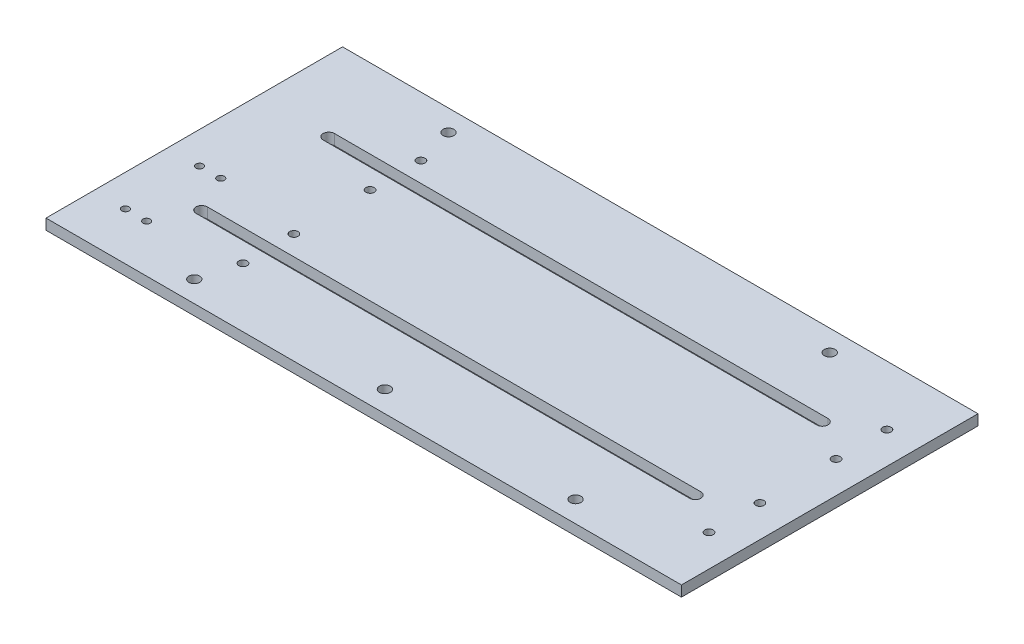
SolidWorks part; units mm, degrees
material "6061-T6 (SS)"
ref_plane "Front Plane" through (0, 0, 0) normal (0, 0, 1) x (1, 0, 0)
ref_plane "Top Plane" through (0, 0, 0) normal (0, 1, 0) x (1, 0, 0)
ref_plane "Right Plane" through (0, 0, 0) normal (1, 0, 0) x (0, 0, -1)
sketch "Sketch1" plane through (0, 0, 0) normal (0, 1, 0) x (1, 0, 0)
  line L1 (-190.5, -88.9) -> (190.5, -88.9)
  line L2 (-190.5, -88.9) -> (-190.5, 88.9)
  line L3 (-190.5, 88.9) -> (190.5, 88.9)
  line L4 (190.5, -88.9) -> (190.5, 88.9)
  point P4 (0, 88.9)
  point P6 (-190.5, 0)
  dimension "D1" = 381
  dimension "D2" = 177.8
extrude "Plate" add sketch "Sketch1" along normal blind 6.35
sketch "Sketch2" plane through (0, 0, 88.9) normal (0, 0, 1) x (1, 0, 0)
  line L1 (-190.5, 0) -> (190.5, 0)
  line L2 (-190.5, 0) -> (-190.5, 31.75)
  line L3 (-190.5, 31.75) -> (190.5, 31.75)
  line L4 (190.5, 0) -> (190.5, 31.75)
  dimension "D1" = 31.75
extrude "Boss-Extrude2" [suppressed] add sketch "Sketch2" along normal blind 6.35
sketch "Sketch3" [suppressed] plane through (0, 0, 95.25) normal (0, 0, 1) x (1, 0, 0)
  line L0 (0, 0) -> (0, 31.75) construction
  line L1 (-190.5, 0) -> (190.5, 0) construction
  line L2 (190.5, 31.75) -> (-190.5, 31.75) construction
  circle A0 centre (0, 19.05) radius 3.175
  circle A1 centre (-127, 19.05) radius 3.175
  circle A2 centre (127, 19.05) radius 3.175
  dimension "D1" = 6.35
  dimension "D2" = 12.7
  dimension "D3" = 127
  dimension "D4" = 127
extrude "Cut-Extrude1" [suppressed] cut sketch "Sketch3" against normal up to surface (6.35 mm away)
sketch "Sketch4" plane through (0, 0, 0) normal (0, -1, 0) x (1, 0, 0)
  line L2 (190.5, -88.9) -> (-190.5, -88.9) construction
  circle A0 centre (0, 76.2) radius 3.2639
  circle A1 centre (-114.3, 76.2) radius 3.2639
  circle A2 centre (114.3, 76.2) radius 3.2639
  circle A3 centre (-114.3, -76.2) radius 3.2639
  circle A5 centre (114.3, -76.2) radius 3.2639
  dimension "D2" = 6.5278
  dimension "D3" = 114.3
  dimension "D5" = 12.7
  dimension "D1" = 76.2
  dimension "D4" = 114.3
extrude "ChassisMountingHoles" cut sketch "Sketch4" against normal up to surface (6.35 mm away) up to face at (0, 6.35, 0)
sketch "Sketch5" plane through (0, 0, 0) normal (0, -1, 0) x (1, 0, 0)
  line L0 (190.5, 88.9) -> (190.5, -88.9) construction
  line L3 (0, 0) -> (0, 229.4543) construction
  line L4 (171.45, 22.86) -> (171.45, 53.34) construction
  line L5 (0, 0) -> (353.5615, 0) construction
  circle A2 centre (171.45, 53.34) radius 2.5019
  circle A8 centre (171.45, 22.86) radius 2.5019
  circle A14 centre (-107.95, 53.34) radius 2.5019
  circle A15 centre (-107.95, 22.86) radius 2.5019
  circle A16 centre (171.45, -53.34) radius 2.5019
  circle A17 centre (171.45, -22.86) radius 2.5019
  circle A18 centre (-107.95, -22.86) radius 2.5019
  circle A19 centre (-107.95, -53.34) radius 2.5019
  dimension "D1" = 5.0038
  dimension "D2" = 19.05
  dimension "D5" = 30.48
  dimension "D6" = 279.4
extrude "LeadScrewGuideMounts" cut sketch "Sketch5" against normal up to surface (6.35 mm away) up to face at (114.3, 6.35, -79.4639)
sketch "Sketch6" plane through (0, 0, 0) normal (0, -1, 0) x (1, 0, 0)
  line L0 (-190.5, -88.9) -> (-190.5, 88.9) construction
  line L1 (-190.5, 88.9) -> (190.5, 88.9) construction
  circle A0 centre (-171.45, 60.325) radius 2.1527
  circle A1 centre (-158.75, 60.325) radius 2.1527
  circle A2 centre (-171.45, 15.875) radius 2.1527
  circle A3 centre (-158.75, 15.875) radius 2.1527
  dimension "D3" = 4.3053
  dimension "D1" = 12.7
  dimension "D2" = 19.05
  dimension "D4" = 44.45
  dimension "D5" = 28.575
extrude "LeadScrewMotorMount" cut sketch "Sketch6" against normal up to surface (6.35 mm away) up to face at (-107.95, 6.35, -25.3619)
sketch "Sketch8" plane through (0, 0, 0) normal (0, -1, 0) x (1, 0, 0)
  circle A0 centre (-25.4, 38.1) radius 3.2639
  circle A1 centre (25.4, 38.1) radius 3.2639
  circle A2 centre (76.2, 38.1) radius 3.2639
  dimension "D1" = 6.5278
  dimension "D2" = 38.1
  dimension "D3" = 25.4
  dimension "D4" = 50.8
  dimension "D5" = 101.6
extrude "Cut-Extrude2" cut sketch "Sketch8" against normal through all
mirror "Mirror1" [suppressed] about plane through (0, 0, 0) normal (0, 0, 1)
sketch "Sketch9" [suppressed] plane through (0, 0, 0) normal (0, -1, 0) x (1, 0, 0)
  line L0 (0, 0) -> (280.1167, 0) construction
  line L4 (85.217, 25.4) -> (85.217, 0)
  line L5 (85.217, 0) -> (97.917, 0)
  line L6 (97.917, 0) -> (97.917, 25.4)
  circle A0 centre (148.717, 38.1) radius 6.35
  arc A1 (97.917, 25.4) -> (85.217, 25.4) centre (91.567, 25.4) ccw
  circle A4 centre (76.2, 38.1) radius 3.2639 construction
  dimension "D2" = 72.517
  dimension "D3" = 12.7
  dimension "D4" = 57.15
  dimension "D6" = 12.7
  dimension "D1" = 38.1
  dimension "D5" = 25.4
extrude "Cut-Extrude3" [suppressed] cut sketch "Sketch9" against normal through all
mirror "Mirror2" [suppressed] about plane through (0, 0, 0) normal (0, 0, 1)
sketch "Sketch10" plane through (0, 0, 0) normal (0, -1, 0) x (1, 0, 0)
  line L1 (-25.4, 41.4782) -> (-147.955, 41.4782)
  line L2 (0, 41.4782) -> (-25.4, 41.4782)
  line L3 (0, 41.4782) -> (147.955, 41.4782)
  line L8 (147.955, 34.7218) -> (147.955, 41.4782) construction
  line L9 (-25.4, 38.1) -> (-15.7885, 38.1) construction
  line L11 (-147.955, 34.7218) -> (147.955, 34.7218)
  circle A2 centre (-25.4, 38.1) radius 3.2639 construction
  circle A3 centre (-25.4, 38.1) radius 3.2639 construction
  arc A7 (147.955, 41.4782) -> (147.955, 34.7218) centre (147.955, 38.1) cw
  arc A8 (-147.955, 34.7218) -> (-147.955, 41.4782) centre (-147.955, 38.1) cw
  point P9 (0, 34.7218)
  dimension "D1" = 295.91
  dimension "D4" = 3.3782
  dimension "D5" = 3.3782
  dimension "D2" = 147.955
  dimension "D3" = 122.555
  dimension "D6" = 3.3782
  dimension "D7" = 34.7218
  dimension "D8" = 25.4
extrude "Cut-Extrude4" cut sketch "Sketch10" against normal through all
mirror "Mirror3" about plane through (0, 0, 0) normal (0, 0, 1) of "Cut-Extrude4"
